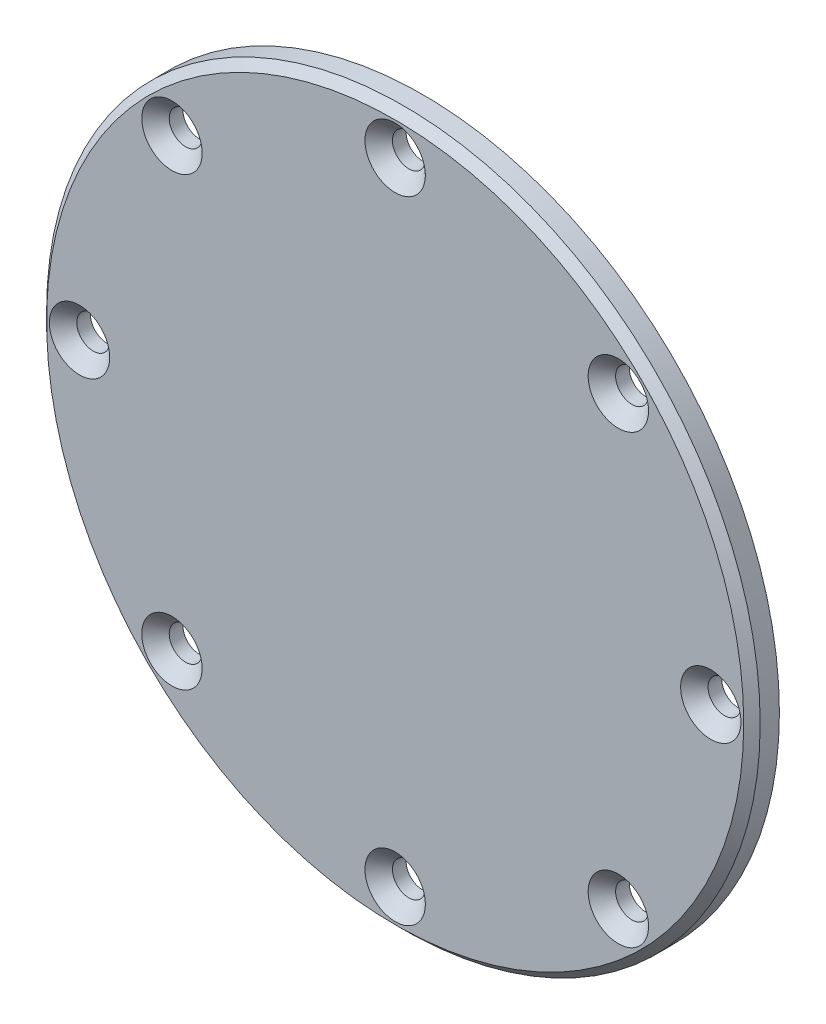
SolidWorks part; units mm, degrees
material "ABS"
ref_plane "Спереди" through (0, 0, 0) normal (0, 0, 1) x (1, 0, 0)
ref_plane "Сверху" through (0, 0, 0) normal (0, 1, 0) x (1, 0, 0)
ref_plane "Справа" through (0, 0, 0) normal (1, 0, 0) x (0, 0, -1)
sketch "Эскиз1" plane through (0, 0, 0) normal (0, 0, 1) x (1, 0, 0)
  circle A0 centre (0, 0) radius 26
  dimension "D1" = 52
extrude "Бобышка-Вытянуть1" add sketch "Эскиз1" along normal blind 2
chamfer "Фаска2" distance 0.6 angle 45 1 edges at (26, 0, 2)
hole_wizard "Зенковка для винта с полупотайной головкой M21" positions "Эскиз2" profile "Эскиз3" countersink size "M2" standard "DIN"
sketch "Эскиз2" plane through (0, 0, 2) normal (0, 0, 1) x (1, 0, 0)
  line L0 (-23, 0) -> (23, 0) construction
  circle A0 centre (0, 0) radius 23 construction
  point P0 (-23, 0)
  dimension "D1" = 46
sketch "Эскиз3" plane through (-23, 0, 2) normal (1, 0, 0) x (0, -1, 0)
  line L0 (0, 0) -> (0, 6.721)
  line L1 (0, 6.721) -> (1.2, 6)
  line L2 (1.2, 6) -> (1.2, 1)
  line L3 (1.2, 1) -> (2.2, 0)
  line L5 (2.2, 0) -> (0, 0)
  line L6 (-1.2, 1) -> (-2.2, 0) construction
  line L10 (0, 6.721) -> (-1.2, 6) construction
  line L11 (0, -6.35) -> (0, 107.95) construction
  dimension "Диаметр отверстия" = 2.4
  dimension "Глубина отверстия" = 6
  dimension "Диаметр передней зенковки" = 4.4
  dimension "Угол передней зенковки" = 90
  dimension "Угол заточки сверла" = 118
pattern_circular "Круговой массив1" count 8 over 360 about axis through (0, 0, 0) along (0, 0, 1) of "Зенковка для винта с полупотайной головкой M21"
